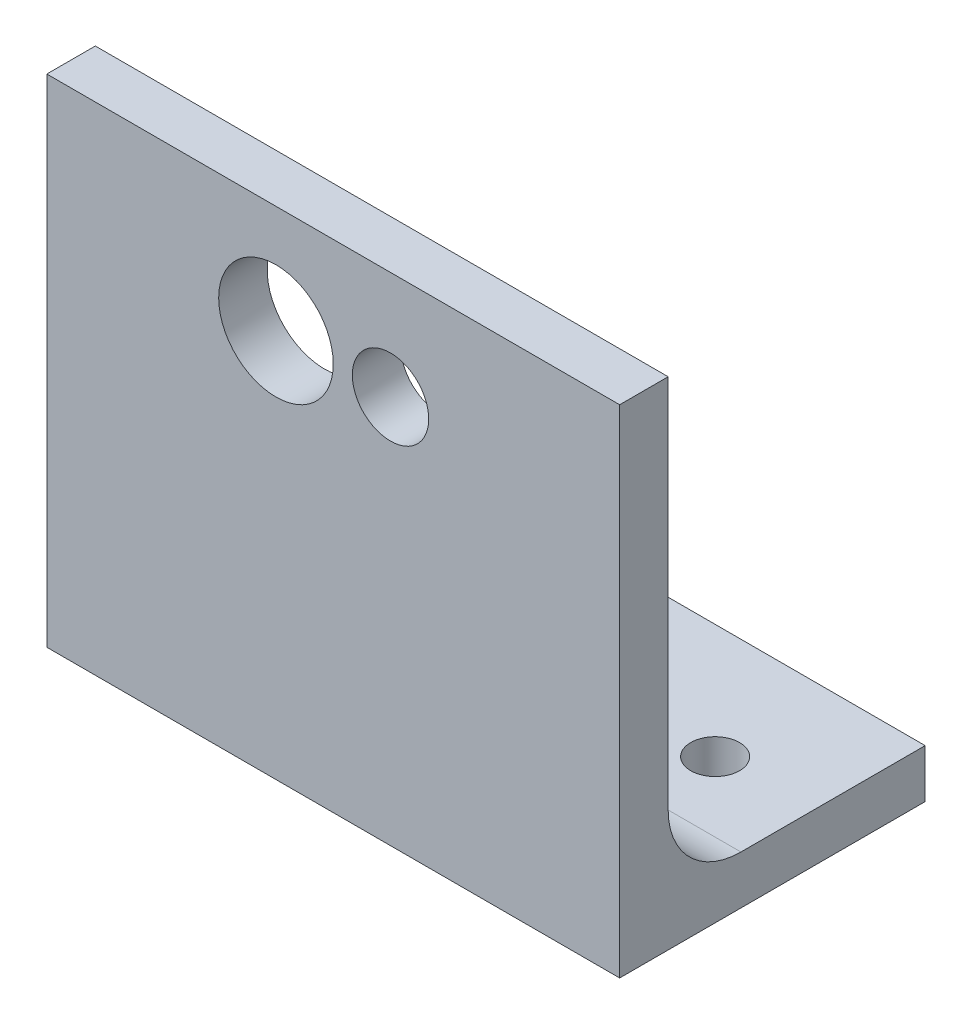
SolidWorks part; units mm, degrees
ref_plane "Front" through (0, 0, 0) normal (0, 0, 1) x (1, 0, 0)
ref_plane "Top" through (0, 0, 0) normal (0, 1, 0) x (1, 0, 0)
ref_plane "Right" through (0, 0, 0) normal (1, 0, 0) x (0, 0, -1)
sketch "Sketch1" plane through (0, 0, 0) normal (1, 0, 0) x (0, 0, -1)
  line L0 (0, 0) -> (0, 88.9)
  line L1 (0, 88.9) -> (6.35, 88.9)
  line L2 (6.35, 88.9) -> (6.35, 15.875)
  line L3 (15.875, 6.35) -> (40, 6.35)
  line L4 (40, 6.35) -> (40, 0)
  line L5 (40, 0) -> (0, 0)
  arc A0 (6.35, 15.875) -> (15.875, 6.35) centre (15.875, 15.875) ccw
  dimension "D3" = 9.525
  dimension "D1" = 40
  dimension "D2" = 6.35
  dimension "D4" = 73.025
  dimension "D5" = 88.9
extrude "Boss-Extrude1" add sketch "Sketch1" along normal blind 75
sketch "Sketch2" plane through (0, 0, 0) normal (0, 0, -1) x (-1, 0, 0)
  line L0 (-45, 50.875) -> (-30, 50.875) construction
  line L1 (-37.5, 50.875) -> (-37.5, 15.875) construction
  line L2 (-75, 0) -> (0, 0) construction
  line L3 (-75, 88.9) -> (0, 88.9)
  line L4 (0, 15.875) -> (0, 88.9)
  line L5 (0, 88.9) -> (-75, 88.9)
  line L6 (-75, 88.9) -> (-75, 15.875)
  line L7 (-75, 15.875) -> (0, 15.875)
  line L8 (0, 15.875) -> (0, 88.9) construction
  line L9 (0, 88.9) -> (-75, 88.9) construction
  line L10 (-75, 88.9) -> (-75, 15.875) construction
  line L11 (-75, 15.875) -> (0, 15.875) construction
  line L12 (-75, 88.9) -> (-75, 65)
  line L13 (-75, 65) -> (0, 65)
  line L14 (0, 88.9) -> (0, 65)
  circle A1 centre (-30, 50.875) radius 7.5
  circle A2 centre (-45, 50.875) radius 5
  point P18 (-34.5214, 28.9918)
  dimension "D2" = 10
  dimension "D4" = 15
  dimension "D5" = 15
  dimension "D3" = 35
  dimension "D6" = 65
  dimension "D1" = 0
extrude "Cut-Extrude1" cut sketch "Sketch2" along normal blind 75
sketch "Sketch3" plane through (0, 0, 0) normal (0, -1, 0) x (1, 0, 0)
  line L0 (12.5, -25) -> (62.5, -25) construction
  line L2 (37.5, -25) -> (37.5, -40) construction
  line L3 (75, -40) -> (0, -40) construction
  point P7 (37.5, -25)
  dimension "D1" = 15
  dimension "D2" = 50
hole_wizard "M6 Clearance Hole1" positions "3DSketch1" profile "Sketch4" hole size "M6" standard "ANSI Metric" end condition through all
sketch3d "3DSketch1"
  point P0 (12.5, 0, -25)
  point P3 (62.5, 0, -25)
sketch "Sketch4" plane through (12.5, 0, -25) normal (1, 0, 0) x (0, 0, -1)
  line L0 (0, 0) -> (0, 65)
  line L1 (0, 65) -> (3.2, 65)
  line L2 (3.2, 65) -> (3.2, 0)
  line L5 (3.2, 0) -> (0, 0)
  line L11 (0, -6.35) -> (0, 107.95) construction
  dimension "Thru Hole Dia." = 6.4
  dimension "Thru Hole Depth" = 65
